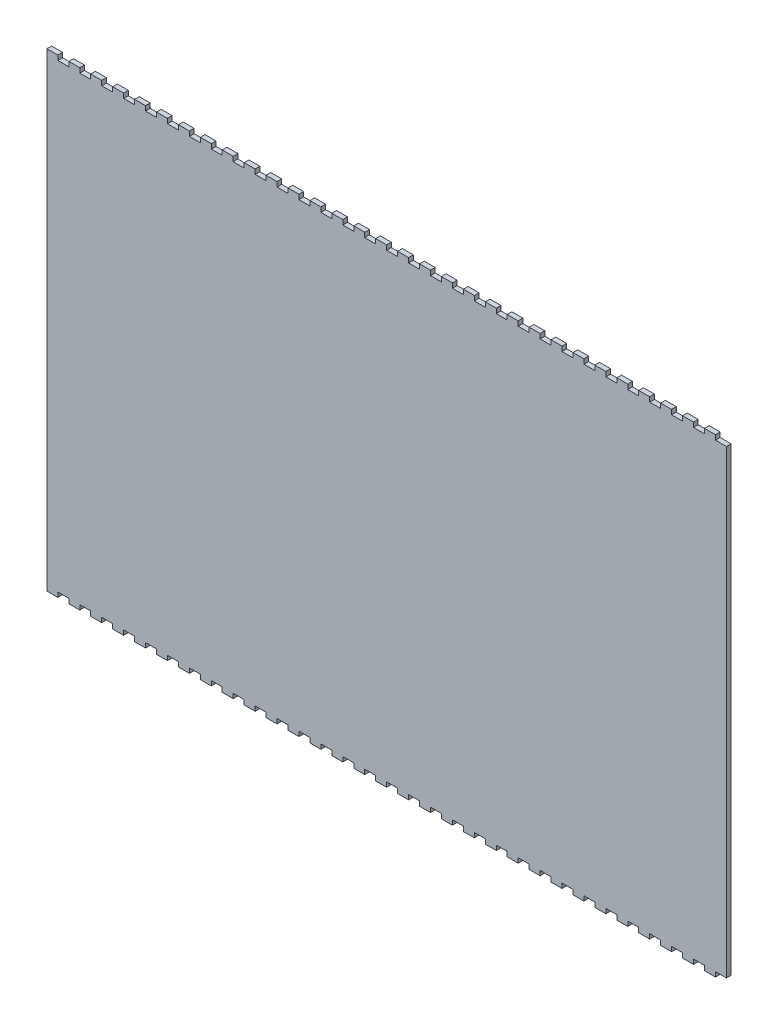
SolidWorks part; units mm, degrees
ref_plane "Plan de face" through (0, 0, 0) normal (0, 0, 1) x (1, 0, 0)
ref_plane "Plan de dessus" through (0, 0, 0) normal (0, 1, 0) x (1, 0, 0)
ref_plane "Plan de droite" through (0, 0, 0) normal (1, 0, 0) x (0, 0, -1)
sketch "Esquisse1" plane through (0, 0, 0) normal (0, 0, 1) x (1, 0, 0)
  line L1 (-217, 150) -> (217, 150)
  line L2 (-217, 150) -> (-217, -150)
  line L3 (-217, -150) -> (217, -150)
  line L4 (217, 150) -> (217, -150)
  line L5 (-217, 150) -> (217, -150) construction
  line L6 (-217, -150) -> (217, 150) construction
  point P0 (0, 0)
  dimension "D1" = 434
  dimension "D2" = 300
extrude "Boss.-Extru.1" add sketch "Esquisse1" along normal blind 3
sketch "Esquisse2" plane through (0, 0, 3) normal (0, 0, 1) x (1, 0, 0)
  line L0 (-217, 0) -> (217, 0) construction
  line L1 (-217, 150) -> (-217, -150) construction
  line L2 (217, -150) -> (217, 150) construction
  line L3 (217, 150) -> (-217, 150) construction
  line L4 (-210, 150) -> (-203, 150)
  line L5 (-210, 150) -> (-210, 147)
  line L6 (-210, 147) -> (-203, 147)
  line L7 (-203, 150) -> (-203, 147)
  line L8 (-196, 150) -> (-196, 147)
  line L9 (-196, 150) -> (-189, 150)
  line L10 (-189, 150) -> (-189, 147)
  line L11 (-196, 147) -> (-189, 147)
  line L12 (-182, 150) -> (-182, 147)
  line L13 (-182, 150) -> (-175, 150)
  line L14 (-175, 150) -> (-175, 147)
  line L15 (-182, 147) -> (-175, 147)
  line L16 (-168, 150) -> (-168, 147)
  line L17 (-168, 150) -> (-161, 150)
  line L18 (-161, 150) -> (-161, 147)
  line L19 (-168, 147) -> (-161, 147)
  line L20 (-154, 150) -> (-154, 147)
  line L21 (-154, 150) -> (-147, 150)
  line L22 (-147, 150) -> (-147, 147)
  line L23 (-154, 147) -> (-147, 147)
  line L24 (-140, 150) -> (-140, 147)
  line L25 (-140, 150) -> (-133, 150)
  line L26 (-133, 150) -> (-133, 147)
  line L27 (-140, 147) -> (-133, 147)
  line L28 (-126, 150) -> (-126, 147)
  line L29 (-126, 150) -> (-119, 150)
  line L30 (-119, 150) -> (-119, 147)
  line L31 (-126, 147) -> (-119, 147)
  line L32 (-112, 150) -> (-112, 147)
  line L33 (-112, 150) -> (-105, 150)
  line L34 (-105, 150) -> (-105, 147)
  line L35 (-112, 147) -> (-105, 147)
  line L36 (-98, 150) -> (-98, 147)
  line L37 (-98, 150) -> (-91, 150)
  line L38 (-91, 150) -> (-91, 147)
  line L39 (-98, 147) -> (-91, 147)
  line L40 (-84, 150) -> (-84, 147)
  line L41 (-84, 150) -> (-77, 150)
  line L42 (-77, 150) -> (-77, 147)
  line L43 (-84, 147) -> (-77, 147)
  line L44 (-70, 150) -> (-70, 147)
  line L45 (-70, 150) -> (-63, 150)
  line L46 (-63, 150) -> (-63, 147)
  line L47 (-70, 147) -> (-63, 147)
  line L48 (-56, 150) -> (-56, 147)
  line L49 (-56, 150) -> (-49, 150)
  line L50 (-49, 150) -> (-49, 147)
  line L51 (-56, 147) -> (-49, 147)
  line L52 (-42, 150) -> (-42, 147)
  line L53 (-42, 150) -> (-35, 150)
  line L54 (-35, 150) -> (-35, 147)
  line L55 (-42, 147) -> (-35, 147)
  line L56 (-28, 150) -> (-28, 147)
  line L57 (-28, 150) -> (-21, 150)
  line L58 (-21, 150) -> (-21, 147)
  line L59 (-28, 147) -> (-21, 147)
  line L60 (-14, 150) -> (-14, 147)
  line L61 (-14, 150) -> (-7, 150)
  line L62 (-7, 150) -> (-7, 147)
  line L63 (-14, 147) -> (-7, 147)
  line L64 (0, 150) -> (0, 147)
  line L65 (0, 150) -> (7, 150)
  line L66 (7, 150) -> (7, 147)
  line L67 (0, 147) -> (7, 147)
  line L68 (14, 150) -> (14, 147)
  line L69 (14, 150) -> (21, 150)
  line L70 (21, 150) -> (21, 147)
  line L71 (14, 147) -> (21, 147)
  line L72 (28, 150) -> (28, 147)
  line L73 (28, 150) -> (35, 150)
  line L74 (35, 150) -> (35, 147)
  line L75 (28, 147) -> (35, 147)
  line L76 (42, 150) -> (42, 147)
  line L77 (42, 150) -> (49, 150)
  line L78 (49, 150) -> (49, 147)
  line L79 (42, 147) -> (49, 147)
  line L80 (56, 150) -> (56, 147)
  line L81 (56, 150) -> (63, 150)
  line L82 (63, 150) -> (63, 147)
  line L83 (56, 147) -> (63, 147)
  line L84 (70, 150) -> (70, 147)
  line L85 (70, 150) -> (77, 150)
  line L86 (77, 150) -> (77, 147)
  line L87 (70, 147) -> (77, 147)
  line L88 (84, 150) -> (84, 147)
  line L89 (84, 150) -> (91, 150)
  line L90 (91, 150) -> (91, 147)
  line L91 (84, 147) -> (91, 147)
  line L92 (98, 150) -> (98, 147)
  line L93 (98, 150) -> (105, 150)
  line L94 (105, 150) -> (105, 147)
  line L95 (98, 147) -> (105, 147)
  line L96 (112, 150) -> (112, 147)
  line L97 (112, 150) -> (119, 150)
  line L98 (119, 150) -> (119, 147)
  line L99 (112, 147) -> (119, 147)
  line L100 (126, 150) -> (126, 147)
  line L101 (126, 150) -> (133, 150)
  line L102 (133, 150) -> (133, 147)
  line L103 (126, 147) -> (133, 147)
  line L104 (140, 150) -> (140, 147)
  line L105 (140, 150) -> (147, 150)
  line L106 (147, 150) -> (147, 147)
  line L107 (140, 147) -> (147, 147)
  line L108 (154, 150) -> (154, 147)
  line L109 (154, 150) -> (161, 150)
  line L110 (161, 150) -> (161, 147)
  line L111 (154, 147) -> (161, 147)
  line L112 (168, 150) -> (168, 147)
  line L113 (168, 150) -> (175, 150)
  line L114 (175, 150) -> (175, 147)
  line L115 (168, 147) -> (175, 147)
  line L116 (182, 150) -> (182, 147)
  line L117 (182, 150) -> (189, 150)
  line L118 (189, 150) -> (189, 147)
  line L119 (182, 147) -> (189, 147)
  line L120 (196, 150) -> (196, 147)
  line L121 (196, 150) -> (203, 150)
  line L122 (203, 150) -> (203, 147)
  line L123 (196, 147) -> (203, 147)
  line L124 (210, 150) -> (210, 147)
  line L125 (210, 150) -> (217, 150)
  line L126 (217, 150) -> (217, 147)
  line L127 (210, 147) -> (217, 147)
  line L128 (210, -147) -> (217, -147)
  line L129 (217, -150) -> (217, -147)
  line L130 (210, -150) -> (217, -150)
  line L131 (210, -150) -> (210, -147)
  line L132 (196, -147) -> (203, -147)
  line L133 (203, -150) -> (203, -147)
  line L134 (196, -150) -> (203, -150)
  line L135 (196, -150) -> (196, -147)
  line L136 (182, -147) -> (189, -147)
  line L137 (189, -150) -> (189, -147)
  line L138 (182, -150) -> (189, -150)
  line L139 (182, -150) -> (182, -147)
  line L140 (168, -147) -> (175, -147)
  line L141 (175, -150) -> (175, -147)
  line L142 (168, -150) -> (175, -150)
  line L143 (168, -150) -> (168, -147)
  line L144 (154, -147) -> (161, -147)
  line L145 (161, -150) -> (161, -147)
  line L146 (154, -150) -> (161, -150)
  line L147 (154, -150) -> (154, -147)
  line L148 (140, -147) -> (147, -147)
  line L149 (147, -150) -> (147, -147)
  line L150 (140, -150) -> (147, -150)
  line L151 (140, -150) -> (140, -147)
  line L152 (126, -147) -> (133, -147)
  line L153 (133, -150) -> (133, -147)
  line L154 (126, -150) -> (133, -150)
  line L155 (126, -150) -> (126, -147)
  line L156 (112, -147) -> (119, -147)
  line L157 (119, -150) -> (119, -147)
  line L158 (112, -150) -> (119, -150)
  line L159 (112, -150) -> (112, -147)
  line L160 (98, -147) -> (105, -147)
  line L161 (105, -150) -> (105, -147)
  line L162 (98, -150) -> (105, -150)
  line L163 (98, -150) -> (98, -147)
  line L164 (84, -147) -> (91, -147)
  line L165 (91, -150) -> (91, -147)
  line L166 (84, -150) -> (91, -150)
  line L167 (84, -150) -> (84, -147)
  line L168 (70, -147) -> (77, -147)
  line L169 (77, -150) -> (77, -147)
  line L170 (70, -150) -> (77, -150)
  line L171 (70, -150) -> (70, -147)
  line L172 (56, -147) -> (63, -147)
  line L173 (63, -150) -> (63, -147)
  line L174 (56, -150) -> (63, -150)
  line L175 (56, -150) -> (56, -147)
  line L176 (42, -147) -> (49, -147)
  line L177 (49, -150) -> (49, -147)
  line L178 (42, -150) -> (49, -150)
  line L179 (42, -150) -> (42, -147)
  line L180 (28, -147) -> (35, -147)
  line L181 (35, -150) -> (35, -147)
  line L182 (28, -150) -> (35, -150)
  line L183 (28, -150) -> (28, -147)
  line L184 (14, -147) -> (21, -147)
  line L185 (21, -150) -> (21, -147)
  line L186 (14, -150) -> (21, -150)
  line L187 (14, -150) -> (14, -147)
  line L188 (0, -147) -> (7, -147)
  line L189 (7, -150) -> (7, -147)
  line L190 (0, -150) -> (7, -150)
  line L191 (0, -150) -> (0, -147)
  line L192 (-14, -147) -> (-7, -147)
  line L193 (-7, -150) -> (-7, -147)
  line L194 (-14, -150) -> (-7, -150)
  line L195 (-14, -150) -> (-14, -147)
  line L196 (-28, -147) -> (-21, -147)
  line L197 (-21, -150) -> (-21, -147)
  line L198 (-28, -150) -> (-21, -150)
  line L199 (-28, -150) -> (-28, -147)
  line L200 (-42, -147) -> (-35, -147)
  line L201 (-35, -150) -> (-35, -147)
  line L202 (-42, -150) -> (-35, -150)
  line L203 (-42, -150) -> (-42, -147)
  line L204 (-56, -147) -> (-49, -147)
  line L205 (-49, -150) -> (-49, -147)
  line L206 (-56, -150) -> (-49, -150)
  line L207 (-56, -150) -> (-56, -147)
  line L208 (-70, -147) -> (-63, -147)
  line L209 (-63, -150) -> (-63, -147)
  line L210 (-70, -150) -> (-63, -150)
  line L211 (-70, -150) -> (-70, -147)
  line L212 (-84, -147) -> (-77, -147)
  line L213 (-77, -150) -> (-77, -147)
  line L214 (-84, -150) -> (-77, -150)
  line L215 (-84, -150) -> (-84, -147)
  line L216 (-98, -147) -> (-91, -147)
  line L217 (-91, -150) -> (-91, -147)
  line L218 (-98, -150) -> (-91, -150)
  line L219 (-98, -150) -> (-98, -147)
  line L220 (-112, -147) -> (-105, -147)
  line L221 (-105, -150) -> (-105, -147)
  line L222 (-112, -150) -> (-105, -150)
  line L223 (-112, -150) -> (-112, -147)
  line L224 (-126, -147) -> (-119, -147)
  line L225 (-119, -150) -> (-119, -147)
  line L226 (-126, -150) -> (-119, -150)
  line L227 (-126, -150) -> (-126, -147)
  line L228 (-140, -147) -> (-133, -147)
  line L229 (-133, -150) -> (-133, -147)
  line L230 (-140, -150) -> (-133, -150)
  line L231 (-140, -150) -> (-140, -147)
  line L232 (-154, -147) -> (-147, -147)
  line L233 (-147, -150) -> (-147, -147)
  line L234 (-154, -150) -> (-147, -150)
  line L235 (-154, -150) -> (-154, -147)
  line L236 (-168, -147) -> (-161, -147)
  line L237 (-161, -150) -> (-161, -147)
  line L238 (-168, -150) -> (-161, -150)
  line L239 (-168, -150) -> (-168, -147)
  line L240 (-182, -147) -> (-175, -147)
  line L241 (-175, -150) -> (-175, -147)
  line L242 (-182, -150) -> (-175, -150)
  line L243 (-182, -150) -> (-182, -147)
  line L244 (-196, -147) -> (-189, -147)
  line L245 (-189, -150) -> (-189, -147)
  line L246 (-196, -150) -> (-189, -150)
  line L247 (-196, -150) -> (-196, -147)
  line L248 (-203, -150) -> (-203, -147)
  line L249 (-210, -147) -> (-203, -147)
  line L250 (-210, -150) -> (-210, -147)
  line L251 (-210, -150) -> (-203, -150)
  dimension "D1" = 3
  dimension "D2" = 7
  dimension "D3" = 7
  dimension "D5" = 7
  dimension "D4" = 31
extrude "Enlèv. mat.-Extru.1" cut sketch "Esquisse2" against normal blind 3
